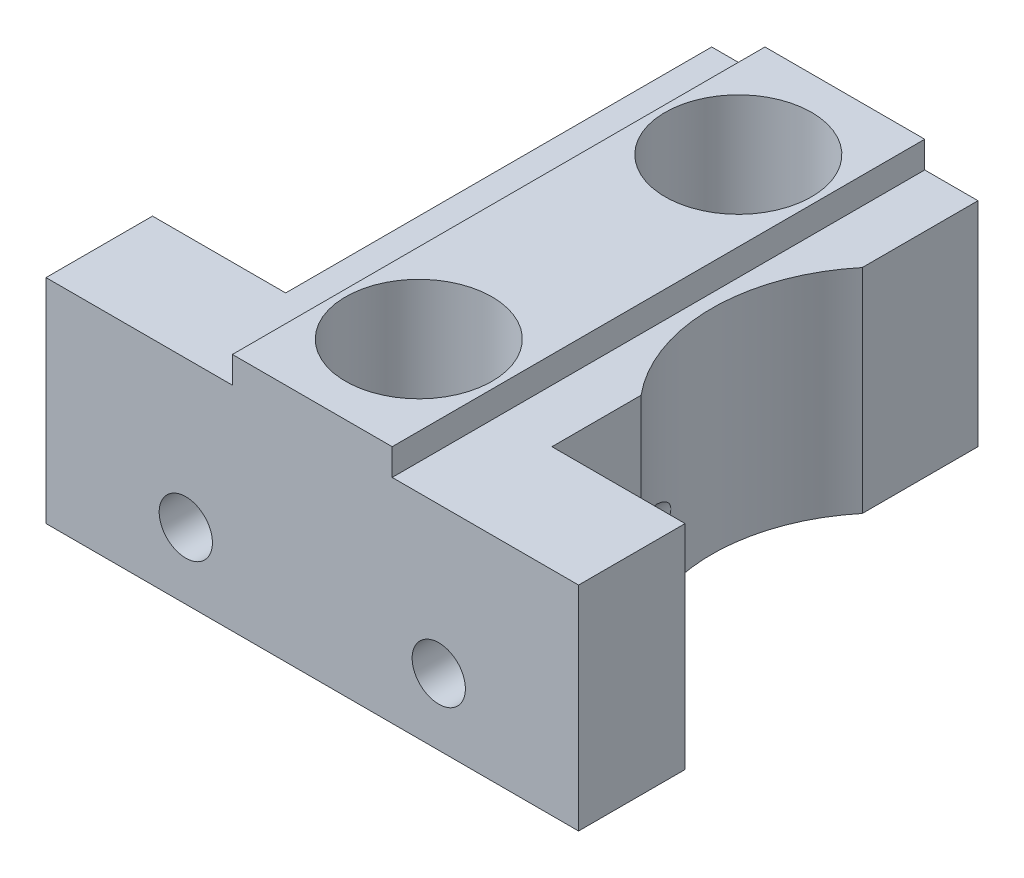
SolidWorks part; units mm, degrees
ref_plane "Front Plane" through (0, 0, 0) normal (0, 0, 1) x (1, 0, 0)
ref_plane "Top Plane" through (0, 0, 0) normal (0, 1, 0) x (1, 0, 0)
ref_plane "Right Plane" through (0, 0, 0) normal (1, 0, 0) x (0, 0, -1)
sketch "Sketch1" plane through (0, 0, 0) normal (0, 1, 0) x (1, 0, 0)
  line L0 (0, 0) -> (0, 20) construction
  line L1 (-10, 0) -> (10, 0)
  line L2 (10, 0) -> (10, 4)
  line L3 (10, 4) -> (5, 4)
  line L4 (5, 4) -> (5, 20)
  line L5 (5, 20) -> (-5, 20)
  line L6 (-5, 20) -> (-5, 4)
  line L7 (-5, 4) -> (-10, 4)
  line L8 (-10, 4) -> (-10, 0)
  dimension "D1" = 10
  dimension "D2" = 4
  dimension "D3" = 20
  dimension "D4" = 20
extrude "Boss-Extrude1" add sketch "Sketch1" along normal blind 8
sketch "Sketch5" plane through (0, 8, 0) normal (0, 1, 0) x (1, 0, 0)
  line L0 (5, 20) -> (-5, 20) construction
  line L1 (-3, 20) -> (3, 20)
  line L2 (-3, 20) -> (-3, 0)
  line L3 (-3, 0) -> (3, 0)
  line L4 (3, 20) -> (3, 0)
  line L5 (-10, 0) -> (10, 0) construction
  dimension "D1" = 6
extrude "Boss-Extrude2" add sketch "Sketch5" along normal blind 1
sketch "Sketch6" plane through (0, 0, 0) normal (0, -1, 0) x (1, 0, 0)
  line L0 (-10, 0) -> (10, 0) construction
  circle A0 centre (10, -11.5) radius 6.5
  dimension "D1" = 13
  dimension "D2" = 10
  dimension "D3" = 11.5
extrude "Cut-Extrude3" cut sketch "Sketch6" against normal through all
sketch "Sketch2" plane through (0, 0, 0) normal (0, -1, 0) x (1, 0, 0)
  line L0 (0, 0) -> (0, -4) construction
  line L1 (0, -4) -> (0, -16) construction
  circle A0 centre (0, -4) radius 2.75
  circle A1 centre (0, -16) radius 2.75
  dimension "D1" = 5.5
  dimension "D2" = 4
  dimension "D3" = 12
extrude "Cut-Extrude1" cut sketch "Sketch2" against normal through all
sketch "Sketch3" plane through (0, 0, 0) normal (0, 0, 1) x (1, 0, 0)
  line L0 (-4.75, 2.5) -> (4.75, 2.5) construction
  line L1 (0, 2.5) -> (0, 0) construction
  circle A0 centre (-4.75, 2.5) radius 1
  circle A1 centre (4.75, 2.5) radius 1
  dimension "D3" = 2
  dimension "D1" = 9.5
  dimension "D2" = 2.5
extrude "Cut-Extrude2" cut sketch "Sketch3" against normal blind 12
